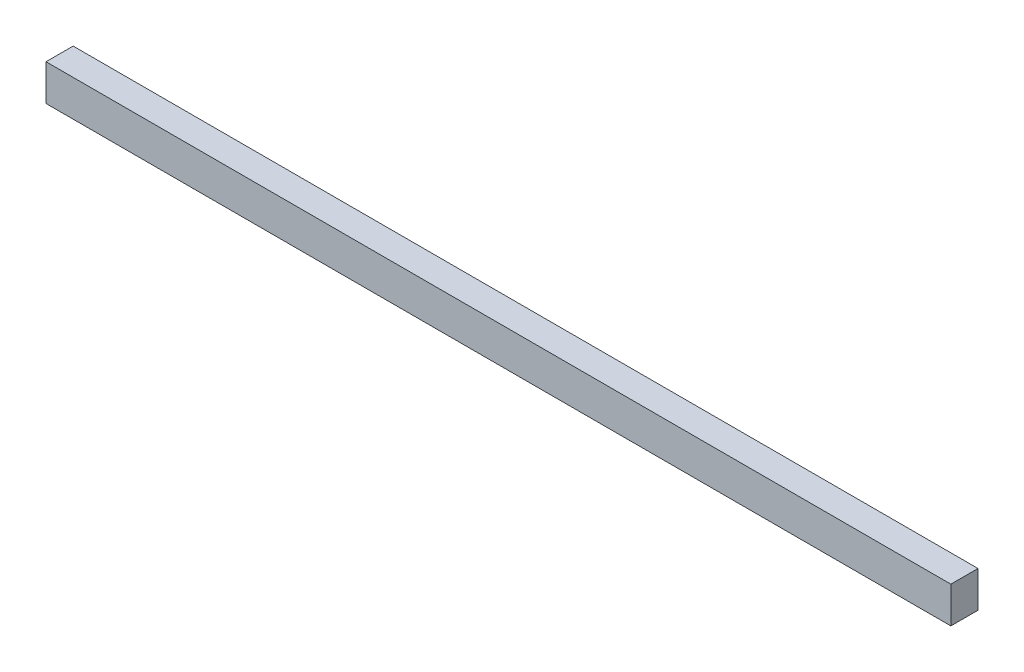
SolidWorks part; units mm, degrees
material "Простая углеродистая сталь"
ref_plane "Спереди" through (0, 0, 0) normal (0, 0, 1) x (1, 0, 0)
ref_plane "Сверху" through (0, 0, 0) normal (0, 1, 0) x (1, 0, 0)
ref_plane "Справа" through (0, 0, 0) normal (1, 0, 0) x (0, 0, -1)
sketch "Эскиз1" plane through (0, 0, 0) normal (1, 0, 0) x (0, 0, -1)
  line L1 (37.5, 50) -> (-37.5, 50)
  line L2 (37.5, 50) -> (37.5, -50)
  line L3 (37.5, -50) -> (-37.5, -50)
  line L4 (-37.5, 50) -> (-37.5, -50)
  line L5 (37.5, 50) -> (-37.5, -50) construction
  line L6 (37.5, -50) -> (-37.5, 50) construction
  point P0 (0, 0)
  dimension "D1" = 75
  dimension "D2" = 100
extrude "Бобышка-Вытянуть1" add sketch "Эскиз1" along normal blind 2500
